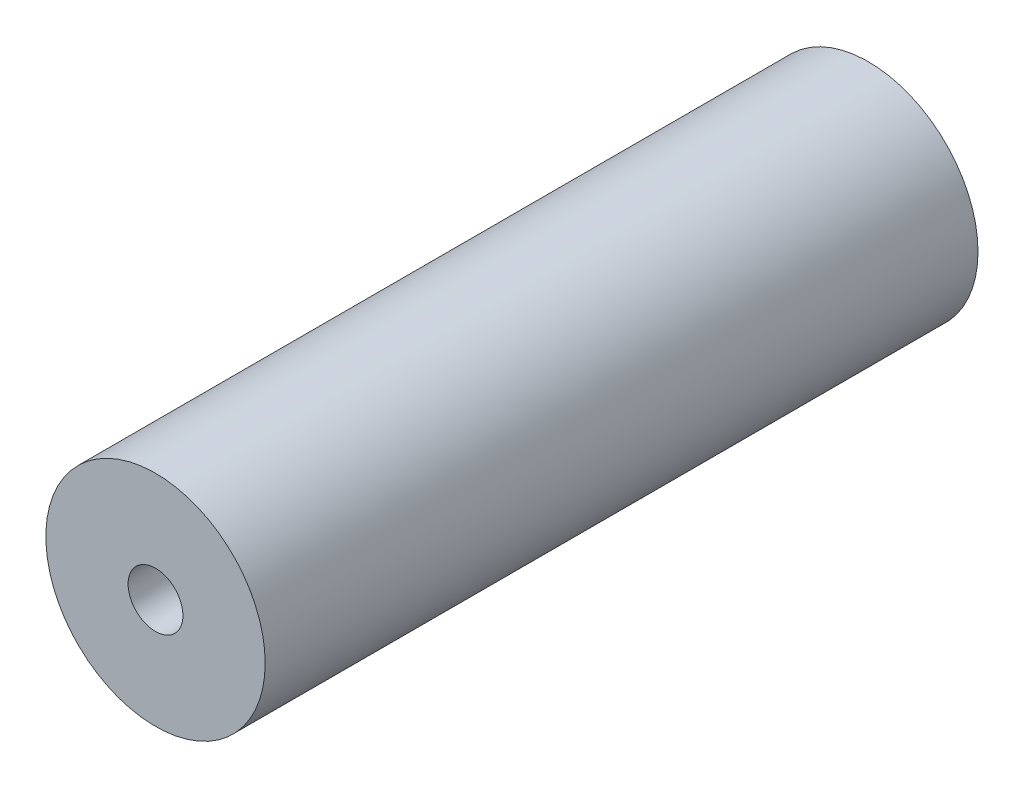
SolidWorks part; units mm, degrees
material "6061-T6 (SS)"
ref_plane "Front Plane" through (0, 0, 0) normal (0, 0, 1) x (1, 0, 0)
ref_plane "Top Plane" through (0, 0, 0) normal (0, 1, 0) x (1, 0, 0)
ref_plane "Right Plane" through (0, 0, 0) normal (1, 0, 0) x (0, 0, -1)
sketch "Sketch1" plane through (0, 0, 0) normal (0, 0, 1) x (1, 0, 0)
  circle A0 centre (0, 0) radius 25.4
  circle A1 centre (0, 0) radius 6.35
  dimension "D1" = 50.8
  dimension "D2" = 12.7
extrude "Boss-Extrude1" add sketch "Sketch1" along normal blind 165.1
